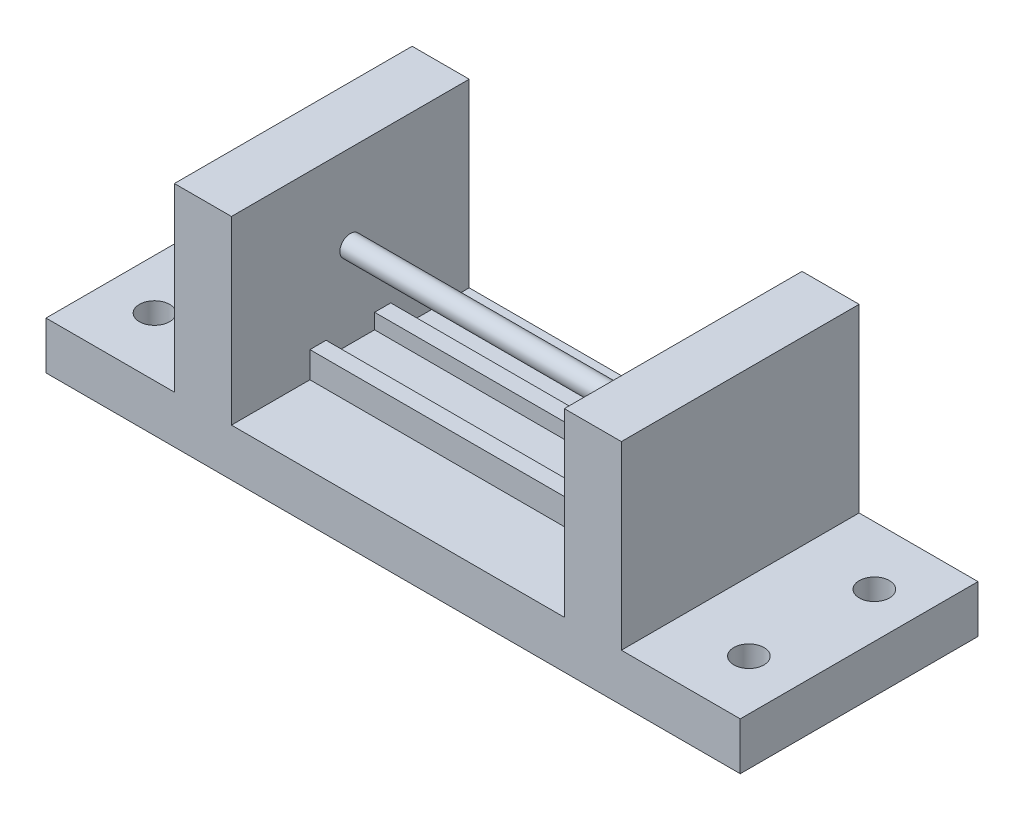
SolidWorks part; units mm, degrees
ref_plane "Front Plane" through (0, 0, 0) normal (0, 0, 1) x (1, 0, 0)
ref_plane "Top Plane" through (0, 0, 0) normal (0, 1, 0) x (1, 0, 0)
ref_plane "Right Plane" through (0, 0, 0) normal (1, 0, 0) x (0, 0, -1)
sketch "Sketch1" plane through (0, 0, 0) normal (0, 1, 0) x (1, 0, 0)
  line L1 (0, 0) -> (146, 0)
  line L2 (0, 0) -> (0, -50)
  line L3 (0, -50) -> (146, -50)
  line L4 (146, 0) -> (146, -50)
  dimension "D1" = 50
  dimension "D2" = 146
extrude "Boss-Extrude1" add sketch "Sketch1" along normal blind 10
sketch "Sketch2" plane through (0, 10, 0) normal (0, 1, 0) x (1, 0, 0)
  line L0 (0, -25) -> (146, -25) construction
  line L5 (146, -50) -> (146, 0) construction
  line L6 (0, 0) -> (0, -50) construction
  line L9 (73, 0) -> (73, -50) construction
  line L10 (146, 0) -> (0, 0) construction
  line L11 (0, -50) -> (146, -50) construction
  circle A0 centre (9.5, -12.3) radius 3.175
  circle A1 centre (10.5, -37.6803) radius 3.175
  dimension "D5" = 6.35
  dimension "D6" = 6.35
  dimension "D1" = 10.5
  dimension "D2" = 12.7
  dimension "D3" = 63.5
  dimension "D7" = 25.4
ref_plane "Plane1" through (73, 0, 0) normal (-1, 0, 0) x (0, 0, 1)
extrude "Cut-Extrude1" cut sketch "Sketch2" against normal blind 10
mirror "Mirror1" about plane through (73, 0, 0) normal (-1, 0, 0) of "Cut-Extrude1"
sketch "Sketch3" plane through (0, 10, 0) normal (0, 1, 0) x (1, 0, 0)
  line L0 (146, 0) -> (0, 0) construction
  line L1 (121, 0) -> (109, 0)
  line L2 (121, 0) -> (121, -50)
  line L3 (121, -50) -> (109, -50)
  line L4 (109, 0) -> (109, -50)
  line L5 (0, -50) -> (146, -50) construction
  line L6 (146, -50) -> (146, 0) construction
  line L7 (27, 0) -> (39, 0)
  line L8 (27, 0) -> (27, -50)
  line L9 (27, -50) -> (39, -50)
  line L10 (39, 0) -> (39, -50)
  dimension "D1" = 12
  dimension "D2" = 12
  dimension "D3" = 70
  dimension "D4" = 25
extrude "Boss-Extrude2" add sketch "Sketch3" along normal blind 38
sketch "Sketch4" plane through (121, 0, 0) normal (1, 0, 0) x (0, 0, -1)
  line L0 (-50, 15) -> (0, 15) construction
  line L1 (-50, 48) -> (-50, 10) construction
  line L2 (0, 48) -> (0, 10) construction
  line L3 (-50, 10) -> (0, 10) construction
  line L4 (-50, 15) -> (-50, 48) construction
  line L5 (-50, 48) -> (0, 48) construction
  line L6 (0, 48) -> (0, 15) construction
  line L8 (-25, 48) -> (-25, 15) construction
  circle A0 centre (-25, 30.2) radius 2.2
  dimension "D2" = 4.4
  dimension "D1" = 5
  dimension "D3" = 17.8
extrude "Boss-Extrude3" add sketch "Sketch4" against normal up to surface (82 mm away) up to face at (39, 29, 25)
sketch "Sketch5" plane through (0, 10, 0) normal (0, 1, 0) x (1, 0, 0)
  line L0 (39, -25) -> (109, -25) construction
  line L1 (39, -50) -> (39, 0) construction
  line L2 (109, 0) -> (109, -50) construction
  line L3 (39, -33.5) -> (39, -16.5)
  line L4 (39, -16.5) -> (109, -16.5)
  line L5 (109, -16.5) -> (109, -33.5)
  line L6 (109, -33.5) -> (39, -33.5)
  point P9 (39, -25)
  dimension "D1" = 17
extrude "Boss-Extrude4" add sketch "Sketch5" along normal blind 5.5
sketch "Sketch6" plane through (0, 15.5, 0) normal (0, 1, 0) x (1, 0, 0)
  line L0 (39, -25) -> (109, -25) construction
  line L1 (39, -16.5) -> (39, -33.5) construction
  line L2 (109, -33.5) -> (109, -16.5) construction
  line L3 (39, -30.1) -> (39, -19.9)
  line L4 (39, -19.9) -> (109, -19.9)
  line L5 (109, -19.9) -> (109, -30.1)
  line L6 (109, -30.1) -> (39, -30.1)
  point P9 (39, -25)
  dimension "D1" = 10.2
extrude "Cut-Extrude2" cut sketch "Sketch6" against normal blind 3.2
sketch "Sketch7" plane through (0, 48, 0) normal (0, 1, 0) x (1, 0, 0)
  line L1 (27, 0) -> (39, 0)
  line L2 (27, 0) -> (27, -50)
  line L3 (27, -50) -> (39, -50)
  line L4 (39, 0) -> (39, -50)
  line L5 (109, 0) -> (121, 0)
  line L6 (109, 0) -> (109, -50)
  line L7 (109, -50) -> (121, -50)
  line L8 (121, 0) -> (121, -50)
